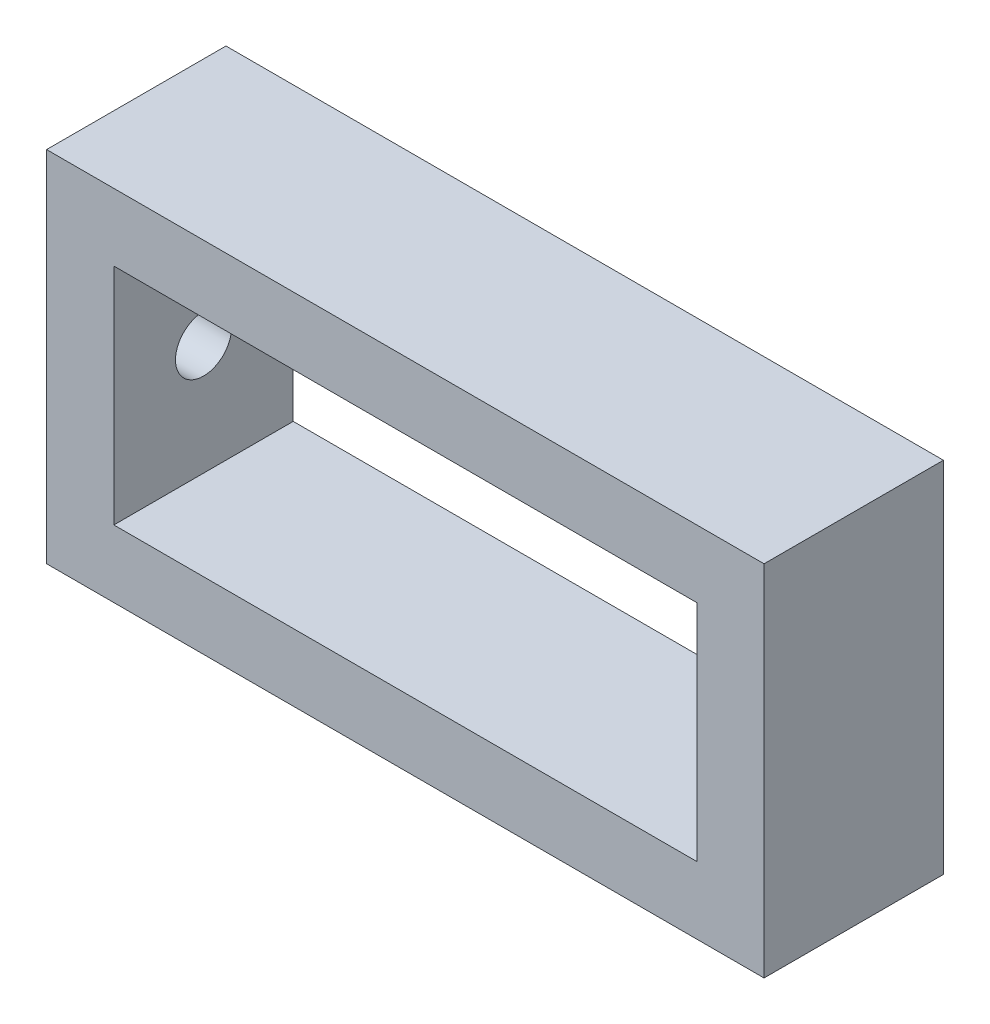
SolidWorks part; units mm, degrees
material "Ductile Iron"
ref_plane "Front Plane" through (0, 0, 0) normal (0, 0, 1) x (1, 0, 0)
ref_plane "Top Plane" through (0, 0, 0) normal (0, 1, 0) x (1, 0, 0)
ref_plane "Right Plane" through (0, 0, 0) normal (1, 0, 0) x (0, 0, -1)
sketch "Sketch1" plane through (0, 0, 0) normal (0, 0, 1) x (1, 0, 0)
  line L0 (19.05, 19.05) -> (19.05, 82.55)
  line L1 (0, 0) -> (203.2, 0)
  line L2 (0, 0) -> (0, 101.6)
  line L3 (0, 101.6) -> (203.2, 101.6)
  line L4 (203.2, 0) -> (203.2, 101.6)
  line L5 (19.05, 82.55) -> (184.15, 82.55)
  line L6 (184.15, 19.05) -> (184.15, 82.55)
  line L7 (19.05, 19.05) -> (184.15, 19.05)
  dimension "D1" = 203.2
  dimension "D2" = 101.6
  dimension "D3" = 19.05
extrude "Boss-Extrude1" add sketch "Sketch1" along normal blind 50.8
sketch "Sketch2" plane through (0, 0, 0) normal (-1, 0, 0) x (0, 0, 1)
  line L0 (0, 101.6) -> (0, 0) construction
  line L1 (50.8, 101.6) -> (0, 101.6) construction
  circle A0 centre (25.4, 50.8) radius 7.9375
  dimension "D1" = 15.875
  dimension "D2" = 25.4
  dimension "D3" = 50.8
extrude "Cut-Extrude1" cut sketch "Sketch2" against normal blind 50.8
